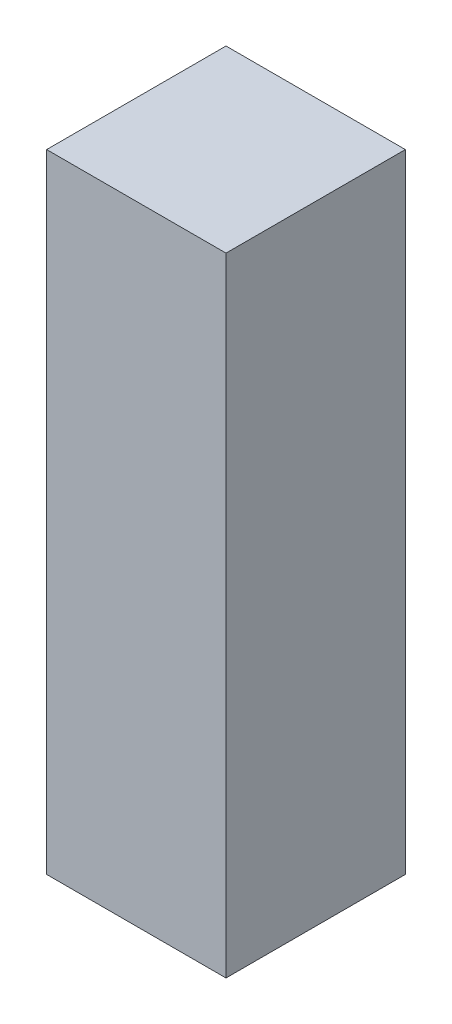
SolidWorks part; units mm, degrees
ref_plane "Спереди" through (0, 0, 0) normal (0, 0, 1) x (1, 0, 0)
ref_plane "Сверху" through (0, 0, 0) normal (0, 1, 0) x (1, 0, 0)
ref_plane "Справа" through (0, 0, 0) normal (1, 0, 0) x (0, 0, -1)
sketch "Эскиз1" plane through (0, 0, 0) normal (0, 1, 0) x (1, 0, 0)
  line L1 (300, 300) -> (-300, 300)
  line L2 (300, 300) -> (300, -300)
  line L3 (300, -300) -> (-300, -300)
  line L4 (-300, 300) -> (-300, -300)
  line L5 (300, 300) -> (-300, -300) construction
  line L6 (300, -300) -> (-300, 300) construction
  point P0 (0, 0)
  dimension "D1" = 600
  dimension "D2" = 600
extrude "Бобышка-Вытянуть1" add sketch "Эскиз1" along normal blind 2100
